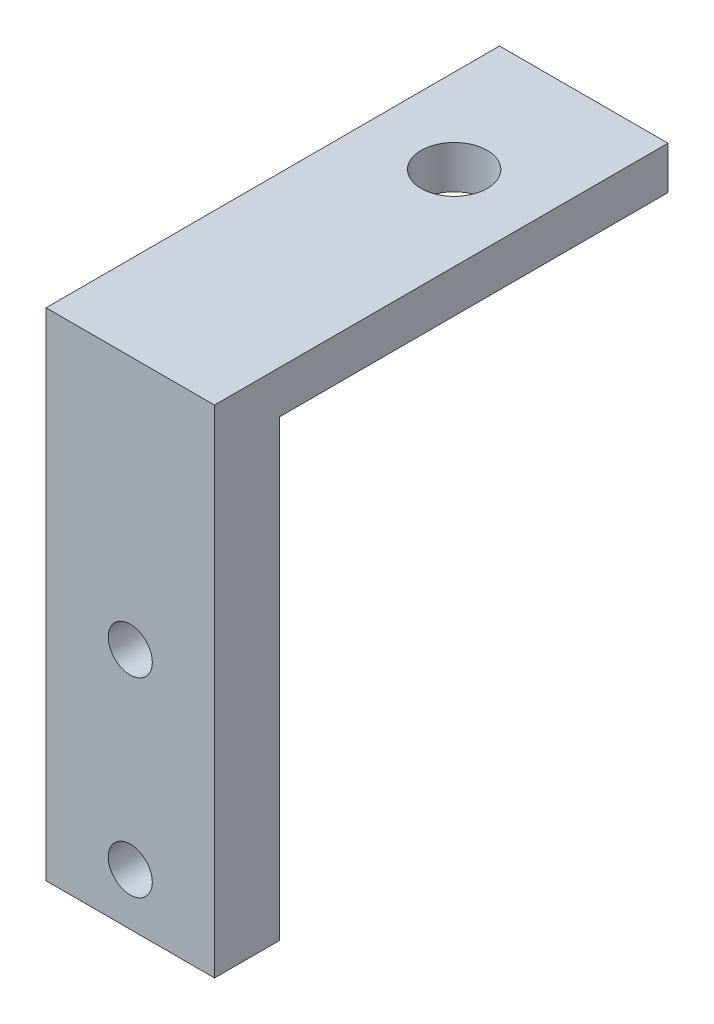
SolidWorks part; units mm, degrees
ref_plane "Front Plane" through (0, 0, 0) normal (0, 0, 1) x (1, 0, 0)
ref_plane "Top Plane" through (0, 0, 0) normal (0, 1, 0) x (1, 0, 0)
ref_plane "Right Plane" through (0, 0, 0) normal (1, 0, 0) x (0, 0, -1)
sketch "Sketch1" plane through (0, 0, 0) normal (1, 0, 0) x (0, 0, -1)
  line L0 (0, 0) -> (0, 38.3)
  line L1 (0, 38.3) -> (35, 38.3)
  line L2 (35, 38.3) -> (35, 35)
  line L3 (35, 35) -> (5, 35)
  line L4 (5, 35) -> (5, 0)
  line L5 (5, 0) -> (0, 0)
  dimension "D1" = 3.3
  dimension "D2" = 5
  dimension "D3" = 35
  dimension "D4" = 30
extrude "Boss-Extrude1" add sketch "Sketch1" along normal blind 13
sketch "Sketch2" plane through (0, 0, -5) normal (0, 0, -1) x (-1, 0, 0)
  line L0 (-13, 0) -> (0, 0) construction
  line L1 (-6.5, 0) -> (-6.5, 18.7) construction
  circle A0 centre (-6.5, 18.7) radius 1.7
  circle A1 centre (-6.5, 4) radius 1.7
  dimension "D3" = 3.4
  dimension "D1" = 14.7
  dimension "D2" = 4
extrude "Cut-Extrude1" cut sketch "Sketch2" against normal through all
sketch "Sketch3" plane through (0, 38.3, 0) normal (0, 1, 0) x (1, 0, 0)
  line L0 (6.5, 35) -> (6.5, 25) construction
  line L1 (13, 35) -> (0, 35) construction
  line L2 (0, 35) -> (0, 15) construction
  line L3 (0, 35) -> (0, 0) construction
  circle A0 centre (6.5, 25) radius 2.55
  point P10 (0, 25)
  dimension "D2" = 5.1
  dimension "D1" = 20
extrude "Cut-Extrude2" cut sketch "Sketch3" against normal through all
